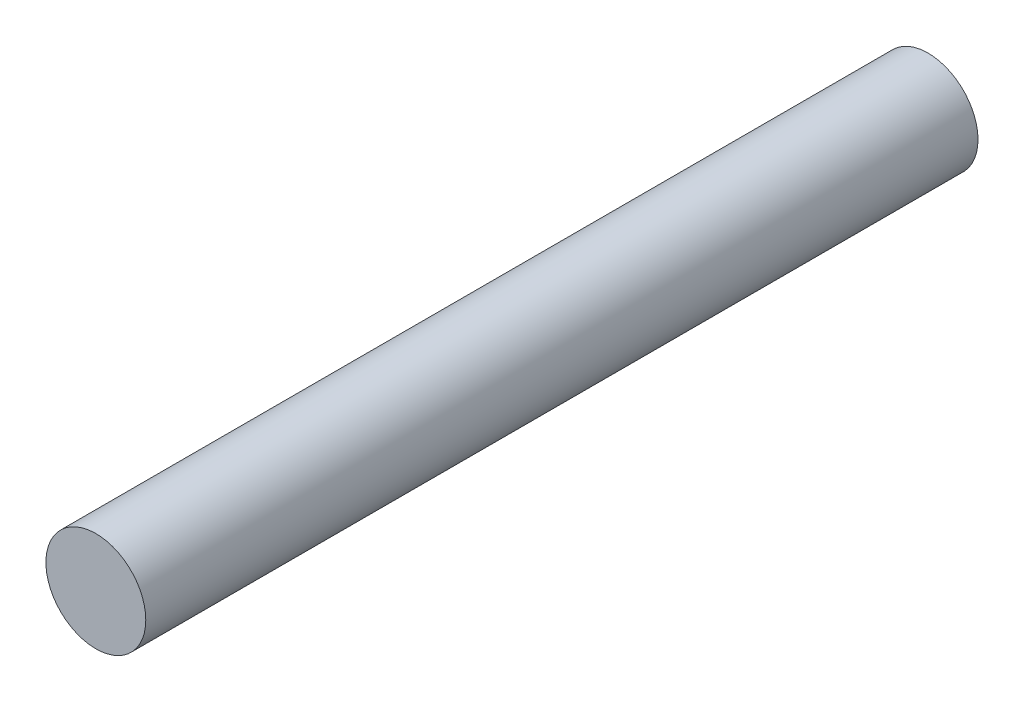
SolidWorks part; units mm, degrees
ref_plane "前视基准面" through (0, 0, 0) normal (0, 0, 1) x (1, 0, 0)
ref_plane "上视基准面" through (0, 0, 0) normal (0, 1, 0) x (1, 0, 0)
ref_plane "右视基准面" through (0, 0, 0) normal (1, 0, 0) x (0, 0, -1)
sketch "草图1" plane through (0, 0, 0) normal (0, 0, 1) x (1, 0, 0)
  circle A0 centre (0, 0) radius 3
  dimension "D1" = 6
extrude "凸台-拉伸1" add sketch "草图1" along normal blind 50
